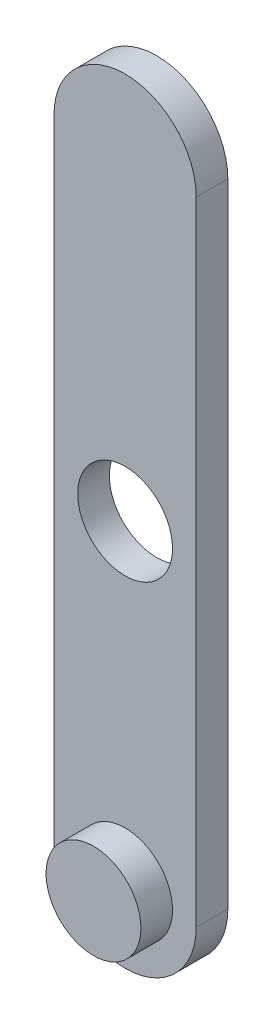
SolidWorks part; units mm, degrees
ref_plane "前视基准面" through (0, 0, 0) normal (0, 0, 1) x (1, 0, 0)
ref_plane "上视基准面" through (0, 0, 0) normal (0, 1, 0) x (1, 0, 0)
ref_plane "右视基准面" through (0, 0, 0) normal (1, 0, 0) x (0, 0, -1)
other "Configuration Table"
sketch "草图1" plane through (0, 0, 0) normal (0, 0, 1) x (1, 0, 0)
  line L0 (0, -20) -> (0, 20) construction
  line L1 (-4.5, -20) -> (-4.5, 20)
  line L2 (4.5, -20) -> (4.5, 20)
  arc A0 (-4.5, -20) -> (4.5, -20) centre (0, -20) ccw
  arc A1 (4.5, 20) -> (-4.5, 20) centre (0, 20) ccw
  circle A2 centre (0, 0) radius 3
  point P2 (0, 0)
extrude "凸台-拉伸1" add sketch "草图1" along normal blind 2
sketch "草图2" plane through (0, 0, 2) normal (0, 0, 1) x (1, 0, 0)
  circle A0 centre (0, -19.8047) radius 3
extrude "凸台-拉伸2" add sketch "草图2" along normal blind 2
